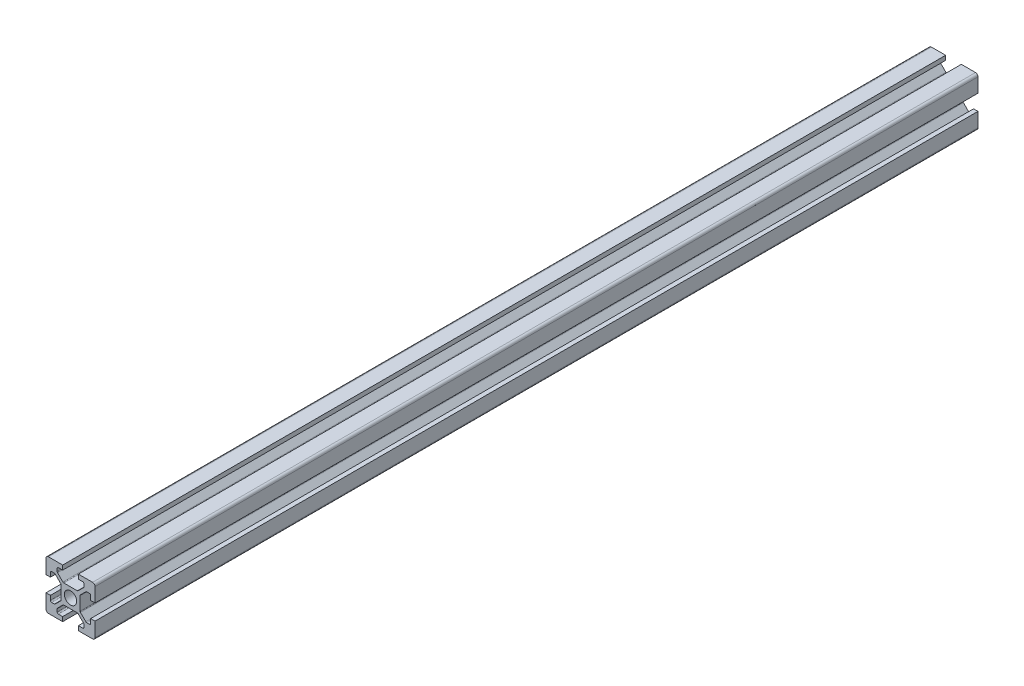
SolidWorks part; units mm, degrees
material "1060 Alloy"
ref_plane "Front Plane" through (0, 0, 0) normal (0, 0, 1) x (1, 0, 0)
ref_plane "Top Plane" through (0, 0, 0) normal (0, 1, 0) x (1, 0, 0)
ref_plane "Right Plane" through (0, 0, 0) normal (1, 0, 0) x (0, 0, -1)
sketch "Sketch1" plane through (0, 0, 0) normal (0, 0, 1) x (1, 0, 0)
  line L0 (20, 0) -> (-8.059, 28.059) construction
  line L1 (0, 0) -> (6.8, 0)
  line L2 (0, 0) -> (0, 6.8)
  line L3 (0, 20) -> (6.8, 20)
  line L4 (20, 0) -> (20, 6.8)
  line L5 (6.8, 20) -> (6.8, 18.2)
  line L6 (20, 20) -> (8.2322, 8.2322) construction
  line L7 (12.95, 6.1) -> (7.05, 6.1)
  line L8 (13.9, 7.05) -> (13.9, 12.95)
  line L9 (12.95, 13.9) -> (7.05, 13.9)
  line L10 (6.1, 7.05) -> (6.1, 12.95)
  line L11 (13.9, 6.1) -> (6.1, 13.9) construction
  line L12 (13.9, 13.9) -> (6.1, 6.1) construction
  line L13 (4.55, 16.4) -> (7.05, 13.9)
  line L14 (13.2, 18.2) -> (13.2, 20)
  line L15 (1.8, 6.8) -> (0, 6.8)
  line L16 (0, 13.2) -> (0, 20)
  line L17 (0, 13.2) -> (1.8, 13.2)
  line L18 (10, 10) -> (10, 13.9) construction
  line L19 (16.4, 4.55) -> (13.9, 7.05)
  line L20 (4.55, 16.4) -> (4.55, 18.2)
  line L21 (4.55, 18.2) -> (6.8, 18.2)
  line L22 (13.2, 18.2) -> (15.45, 18.2)
  line L23 (15.45, 18.2) -> (15.45, 16.4)
  line L24 (15.45, 16.4) -> (12.95, 13.9)
  line L25 (16.4, 4.55) -> (18.2, 4.55)
  line L26 (18.2, 4.55) -> (18.2, 6.8)
  line L27 (20, 6.8) -> (18.2, 6.8)
  line L28 (18.2, 13.2) -> (20, 13.2)
  line L29 (18.2, 13.2) -> (18.2, 15.45)
  line L30 (18.2, 15.45) -> (16.4, 15.45)
  line L31 (16.4, 15.45) -> (13.9, 12.95)
  line L32 (1.8, 4.55) -> (3.6, 4.55)
  line L33 (3.6, 15.45) -> (6.1, 12.95)
  line L34 (3.6, 15.45) -> (1.8, 15.45)
  line L35 (1.8, 15.45) -> (1.8, 13.2)
  line L36 (0, 13.2) -> (1.8, 13.2)
  line L37 (1.8, 6.8) -> (0, 6.8)
  line L38 (3.6, 4.55) -> (6.1, 7.05)
  line L39 (1.8, 6.8) -> (1.8, 4.55)
  line L40 (15.45, 3.6) -> (12.95, 6.1)
  line L41 (4.55, 3.6) -> (7.05, 6.1)
  line L42 (4.55, 1.8) -> (4.55, 3.6)
  line L43 (6.8, 1.8) -> (4.55, 1.8)
  line L44 (6.8, 1.8) -> (6.8, 0)
  line L45 (15.45, 3.6) -> (15.45, 1.8)
  line L46 (15.45, 1.8) -> (13.2, 1.8)
  line L47 (13.2, 0) -> (13.2, 1.8)
  line L48 (13.2, 20) -> (20, 20)
  line L49 (20, 13.2) -> (20, 20)
  line L50 (13.2, 0) -> (20, 0)
  line L51 (6.1, 6.1) -> (-5.5045, -5.5045) construction
  circle A0 centre (10, 10) radius 2.5
  point P25 (10, 16.4)
  point P39 (13.2, 19.1)
  point P46 (0.9, 6.8)
  dimension "D3" = 5
  dimension "D2" = 20
  dimension "D4" = 7.8
  dimension "D5" = 7.8
  dimension "D6" = 6.8
  dimension "D7" = 6.8
  dimension "D8" = 1.8
  dimension "D9" = 10.9
  dimension "D10" = 1.8
  dimension "D11" = 10.9
  dimension "D12" = 20
extrude "Boss-Extrude1" add sketch "Sketch1" along normal blind 360 contours L47 L50 L4 L27 L26 L25 L19 L8 L31 L30 L29 L28 L49 L48 L14 L22 L23 L24 L9 L13 L20 L21 L5 L3 L16 L17 L35 L34 L33 L10 L38 L32 L39 L15 L2 L1 L44 L43 L42 L41 L7 L40 L45 L46 A0
fillet "Fillet1" radius 1 4 edges at (20, 20, 180) (20, 0, 180) (0, 0, 180) (0, 20, 180)
fillet "Fillet2" radius 0.5 6 edges at (4.55, 18.2, 180) (4.55, 16.4, 180) (7.05, 13.9, 180) (15.45, 18.2, 180) (15.45, 16.4, 180) (12.95, 13.9, 180)
fillet "Fillet3" radius 0.5 6 edges at (18.2, 15.45, 180) (16.4, 15.45, 180) (13.9, 12.95, 180) (18.2, 4.55, 180) (13.9, 7.05, 180) (16.4, 4.55, 180)
fillet "Fillet4" radius 0.5 6 edges at (1.8, 15.45, 180) (3.6, 15.45, 180) (6.1, 12.95, 180) (3.6, 4.55, 180) (1.8, 4.55, 180) (6.1, 7.05, 180)
fillet "Fillet5" radius 0.5 6 edges at (7.05, 6.1, 180) (4.55, 3.6, 180) (4.55, 1.8, 180) (15.45, 1.8, 180) (15.45, 3.6, 180) (12.95, 6.1, 180)
